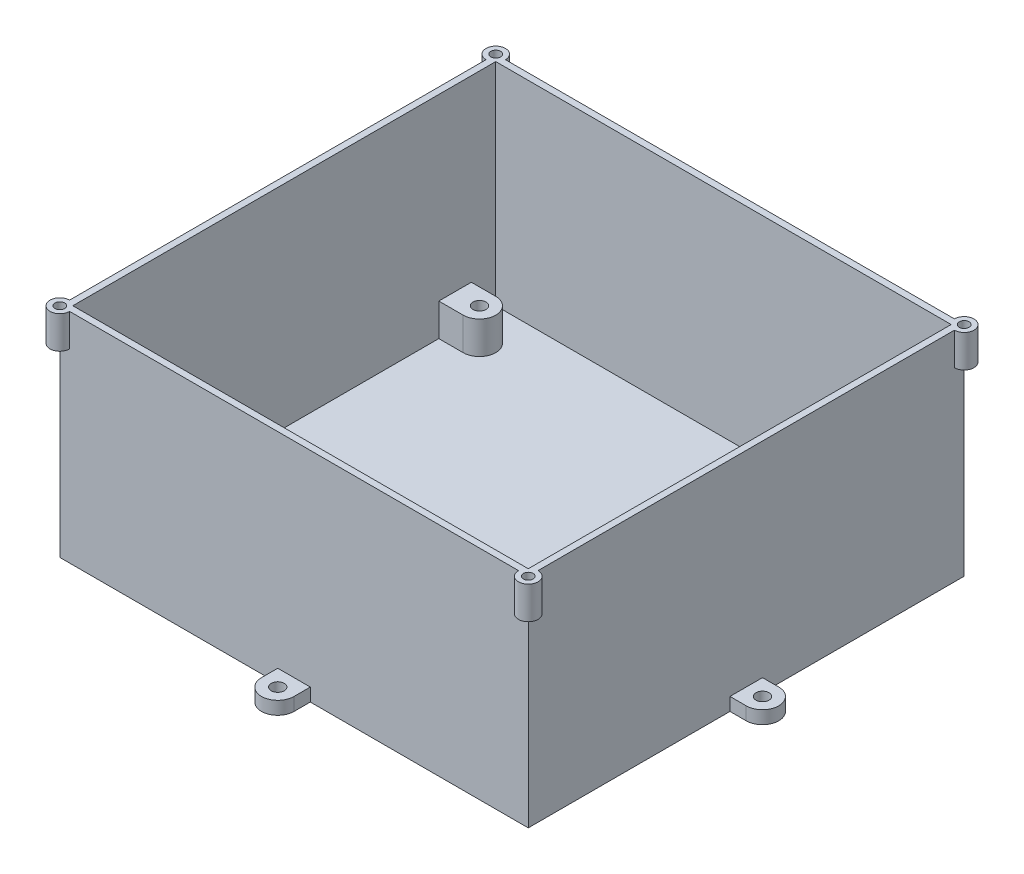
SolidWorks part; units mm, degrees
ref_plane "Front Plane" through (0, 0, 0) normal (0, 0, 1) x (1, 0, 0)
ref_plane "Top Plane" through (0, 0, 0) normal (0, 1, 0) x (1, 0, 0)
ref_plane "Right Plane" through (0, 0, 0) normal (1, 0, 0) x (0, 0, -1)
sketch "Sketch1" plane through (0, 0, 0) normal (0, 1, 0) x (1, 0, 0)
  line L0 (-72, 67) -> (-72, -67)
  line L1 (-70, 65) -> (70, 65)
  line L2 (-70, 65) -> (-70, 57.5)
  line L3 (-70, -65) -> (70, -65)
  line L4 (70, 65) -> (70, 57.5)
  line L5 (-62.5, 52.5) -> (-70, 52.5) construction
  line L6 (-67.5, 57.5) -> (67.5, 57.5) construction
  line L7 (-72, -67) -> (72, -67)
  line L8 (72, 67) -> (72, -67)
  line L9 (-72, 67) -> (72, 67)
  line L10 (-67.5, 57.5) -> (-67.5, -57.5) construction
  line L11 (-67.5, -57.5) -> (67.5, -57.5) construction
  line L12 (67.5, 57.5) -> (67.5, -57.5) construction
  line L13 (-67.5, 57.5) -> (67.5, -57.5) construction
  line L14 (-67.5, -57.5) -> (67.5, 57.5) construction
  line L15 (-62.5, 52.5) -> (-72, 52.5) construction
  line L16 (-62.5, 47.5) -> (-70, 47.5)
  line L17 (-62.5, 57.5) -> (-70, 57.5)
  line L18 (62.5, 52.5) -> (72, 52.5) construction
  line L19 (62.5, 57.5) -> (70, 57.5)
  line L20 (62.5, 47.5) -> (70, 47.5)
  line L21 (62.5, -52.5) -> (72, -52.5) construction
  line L22 (62.5, -47.5) -> (70, -47.5)
  line L23 (62.5, -57.5) -> (70, -57.5)
  line L24 (-62.5, -52.5) -> (-72, -52.5) construction
  line L25 (-62.5, -57.5) -> (-70, -57.5)
  line L26 (-62.5, -47.5) -> (-70, -47.5)
  line L27 (-70, 47.5) -> (-70, -47.5)
  line L28 (-70, 65) -> (-70, -65) construction
  line L29 (70, 47.5) -> (70, -47.5)
  line L30 (70, 65) -> (70, -65) construction
  line L31 (70, -57.5) -> (70, -65)
  line L32 (-70, -57.5) -> (-70, -65)
  circle A0 centre (-62.5, 52.5) radius 2
  circle A1 centre (62.5, 52.5) radius 2
  circle A2 centre (-62.5, -52.5) radius 2
  circle A3 centre (62.5, -52.5) radius 2
  arc A4 (-62.5, 47.5) -> (-62.5, 57.5) centre (-62.5, 52.5) ccw
  arc A6 (62.5, 57.5) -> (62.5, 47.5) centre (62.5, 52.5) ccw
  arc A8 (62.5, -47.5) -> (62.5, -57.5) centre (62.5, -52.5) ccw
  arc A10 (-62.5, -57.5) -> (-62.5, -47.5) centre (-62.5, -52.5) ccw
  point P0 (0, 0)
  point P18 (-67.25, 52.5)
  point P20 (0, 0)
  point P31 (67.25, 52.5)
  point P36 (67.25, -52.5)
  point P42 (-67.25, -52.5)
  dimension "D4" = 4
  dimension "D16" = 5
  dimension "D17" = 5
  dimension "D18" = 5
  dimension "D19" = 5
  dimension "D1" = 130
  dimension "D2" = 140
  dimension "D5" = 125
  dimension "D6" = 105
  dimension "D7" = 5
  dimension "D8" = 5
  dimension "D9" = 135
  dimension "D10" = 115
  dimension "D11" = 5
  dimension "D12" = 5
  dimension "D13" = 105
  dimension "D14" = 5
  dimension "D3" = 2
extrude "Boss-Extrude1" add sketch "Sketch1" along normal blind 55
sketch "Sketch2" plane through (0, 55, 0) normal (0, 1, 0) x (1, 0, 0)
  line L0 (-70, -47.5) -> (-62.5, -47.5) construction
  line L1 (-62.5, -57.5) -> (-70, -57.5) construction
  line L2 (70, -57.5) -> (62.5, -57.5) construction
  line L3 (62.5, -47.5) -> (70, -47.5) construction
  line L4 (70, 47.5) -> (62.5, 47.5) construction
  line L5 (62.5, 57.5) -> (70, 57.5) construction
  line L6 (-62.5, 47.5) -> (-70, 47.5) construction
  line L7 (-70, 57.5) -> (-62.5, 57.5) construction
  line L8 (-70, -47.5) -> (-62.5, -47.5)
  line L9 (-62.5, -57.5) -> (-70, -57.5)
  line L10 (70, -57.5) -> (62.5, -57.5)
  line L11 (62.5, -47.5) -> (70, -47.5)
  line L12 (70, 47.5) -> (62.5, 47.5)
  line L13 (62.5, 57.5) -> (70, 57.5)
  line L14 (-62.5, 47.5) -> (-70, 47.5)
  line L15 (-70, 57.5) -> (-62.5, 57.5)
  line L16 (-70, 57.5) -> (-70, 47.5)
  line L17 (70, 57.5) -> (70, 47.5)
  line L18 (70, -47.5) -> (70, -57.5)
  line L19 (-70, -47.5) -> (-70, -57.5)
  circle A0 centre (62.5, 52.5) radius 2 construction
  circle A1 centre (-62.5, 52.5) radius 2 construction
  circle A2 centre (-62.5, -52.5) radius 2 construction
  arc A3 (-62.5, -57.5) -> (-62.5, -47.5) centre (-62.5, -52.5) ccw construction
  circle A4 centre (62.5, -52.5) radius 2 construction
  arc A5 (62.5, -47.5) -> (62.5, -57.5) centre (62.5, -52.5) ccw construction
  arc A6 (62.5, 57.5) -> (62.5, 47.5) centre (62.5, 52.5) ccw construction
  arc A7 (-62.5, 47.5) -> (-62.5, 57.5) centre (-62.5, 52.5) ccw construction
  circle A8 centre (62.5, 52.5) radius 2
  circle A9 centre (-62.5, 52.5) radius 2
  circle A10 centre (-62.5, -52.5) radius 2
  arc A11 (-62.5, -57.5) -> (-62.5, -47.5) centre (-62.5, -52.5) ccw
  circle A12 centre (62.5, -52.5) radius 2
  arc A13 (62.5, -47.5) -> (62.5, -57.5) centre (62.5, -52.5) ccw
  arc A14 (62.5, 57.5) -> (62.5, 47.5) centre (62.5, 52.5) ccw
  arc A15 (-62.5, 47.5) -> (-62.5, 57.5) centre (-62.5, 52.5) ccw
extrude "Cut-Extrude1" cut sketch "Sketch2" against normal blind 45
sketch "Sketch3" plane through (0, 0, 0) normal (0, -1, 0) x (1, 0, 0)
  line L1 (-72, 67) -> (72, 67)
  line L2 (-72, 67) -> (-72, -67)
  line L3 (-72, -67) -> (72, -67)
  line L4 (72, 67) -> (72, -67)
extrude "Boss-Extrude2" add sketch "Sketch3" along normal blind 2
sketch "Sketch4" plane through (0, 0, 0) normal (0, 1, 0) x (1, 0, 0)
  line L0 (-87.4721, 0) -> (87.4721, 0) construction
  line L1 (0, 80.0878) -> (0, -80.0878) construction
  line L2 (72, 67) -> (-72, 67) construction
  line L3 (72, -67) -> (72, 67) construction
  line L4 (0, 72) -> (0, 65) construction
  line L5 (5, 72) -> (5, 65)
  line L6 (-5, 72) -> (-5, 65)
  line L7 (77, 0) -> (70, 0) construction
  line L8 (77, -5) -> (70, -5)
  line L9 (77, 5) -> (70, 5)
  line L10 (-5, 65) -> (5, 65)
  line L11 (70, 5) -> (70, -5)
  line L12 (-77, -5) -> (-70, -5)
  line L13 (-77, 5) -> (-70, 5)
  line L14 (-70, 5) -> (-70, -5)
  line L15 (-5, -65) -> (5, -65)
  line L16 (5, -72) -> (5, -65)
  line L17 (-5, -72) -> (-5, -65)
  circle A0 centre (0, 72) radius 2
  circle A1 centre (77, 0) radius 2
  arc A2 (5, 72) -> (-5, 72) centre (0, 72) ccw
  arc A4 (77, -5) -> (77, 5) centre (77, 0) ccw
  circle A6 centre (-77, 0) radius 2
  arc A7 (-77, -5) -> (-77, 5) centre (-77, 0) cw
  circle A8 centre (0, -72) radius 2
  arc A9 (5, -72) -> (-5, -72) centre (0, -72) cw
  point P4 (0, 0)
  point P8 (0, 0)
  point P16 (0, 68.5)
  point P23 (73.5, 0)
  dimension "D3" = 4
  dimension "D4" = 4
  dimension "D5" = 5
  dimension "D6" = 5
  dimension "D1" = 5
  dimension "D2" = 5
  dimension "D7" = 7
  dimension "D8" = 7
sketch "Sketch5" plane through (0, -2, 0) normal (0, -1, 0) x (1, 0, 0)
  line L0 (-70, -5) -> (-70, 5) construction
  line L1 (-77, 5) -> (-70, 5) construction
  line L2 (-77, -5) -> (-70, -5) construction
  line L3 (5, -72) -> (5, -65) construction
  line L4 (-5, -65) -> (5, -65) construction
  line L5 (-5, -72) -> (-5, -65) construction
  line L6 (70, -5) -> (70, 5) construction
  line L7 (77, 5) -> (70, 5) construction
  line L8 (77, -5) -> (70, -5) construction
  line L9 (-5, 65) -> (5, 65) construction
  line L10 (5, 72) -> (5, 65) construction
  line L11 (-5, 72) -> (-5, 65) construction
  line L12 (-70, -5) -> (-70, 5)
  line L13 (-77, 5) -> (-70, 5)
  line L14 (-77, -5) -> (-70, -5)
  line L15 (5, -72) -> (5, -65)
  line L16 (-5, -65) -> (5, -65)
  line L17 (-5, -72) -> (-5, -65)
  line L18 (70, -5) -> (70, 5)
  line L19 (77, 5) -> (70, 5)
  line L20 (77, -5) -> (70, -5)
  line L21 (-5, 65) -> (5, 65)
  line L22 (5, 72) -> (5, 65)
  line L23 (-5, 72) -> (-5, 65)
  arc A0 (-77, 5) -> (-77, -5) centre (-77, 0) ccw construction
  arc A1 (-5, -72) -> (5, -72) centre (0, -72) ccw construction
  circle A2 centre (77, 0) radius 2 construction
  arc A3 (77, -5) -> (77, 5) centre (77, 0) ccw construction
  circle A4 centre (0, 72) radius 2 construction
  arc A5 (5, 72) -> (-5, 72) centre (0, 72) ccw construction
  arc A6 (-77, 5) -> (-77, -5) centre (-77, 0) ccw
  arc A7 (-5, -72) -> (5, -72) centre (0, -72) ccw
  circle A8 centre (77, 0) radius 2
  arc A9 (77, -5) -> (77, 5) centre (77, 0) ccw
  circle A10 centre (0, 72) radius 2
  arc A11 (5, 72) -> (-5, 72) centre (0, 72) ccw
  circle A12 centre (-77, 0) radius 2 construction
  circle A13 centre (0, -72) radius 2 construction
  circle A14 centre (-77, 0) radius 2
  circle A15 centre (0, -72) radius 2
extrude "Boss-Extrude4" add sketch "Sketch5" against normal blind 4
sketch "Sketch6" plane through (0, 55, 0) normal (0, 1, 0) x (1, 0, 0)
  line L0 (72, 67) -> (-72, 67) construction
  line L1 (-72, -67) -> (72, -67) construction
  line L2 (72, -67) -> (72, 67) construction
  line L3 (-70, -65) -> (70, -65) construction
  line L4 (70, -65) -> (70, 65) construction
  line L5 (70, 65) -> (-70, 65) construction
  line L6 (-70, 65) -> (-70, -65) construction
  line L7 (-72, 67) -> (-72, -67) construction
  line L8 (72, 67) -> (-72, 67)
  line L9 (-72, -67) -> (72, -67)
  line L10 (72, -67) -> (72, 67)
  line L11 (-70, -65) -> (70, -65)
  line L12 (70, -65) -> (70, 65)
  line L13 (70, 65) -> (-70, 65)
  line L14 (-70, 65) -> (-70, -65)
  line L15 (-72, 67) -> (-72, -67)
extrude "Boss-Extrude5" add sketch "Sketch6" along normal blind 10
sketch "Sketch8" plane through (-72, 0, 0) normal (-1, 0, 0) x (0, 0, 1)
  line L0 (0, 0) -> (0, 72.1803) construction
  line L1 (0, 57.2077) -> (45, 57.2077) construction
  line L2 (0, 57.2077) -> (0, 11.2077) construction
  line L3 (0, 11.2077) -> (45, 11.2077) construction
  line L4 (45, 57.2077) -> (45, 11.2077) construction
  dimension "D1" = 45
  dimension "D2" = 46
  dimension "D3" = 0
sketch "Sketch11" plane through (0, 65, 0) normal (0, 1, 0) x (1, 0, 0)
  line L0 (-72, -67) -> (72, -67) construction
  line L1 (72, -67) -> (72, 67) construction
  line L2 (-72, 67) -> (-72, -67) construction
  line L3 (72, 67) -> (-72, 67) construction
  line L4 (-70.5, -67) -> (-69, -67)
  line L5 (72, -65.5) -> (72, -64)
  line L6 (-72, 65.5) -> (-72, 64)
  line L7 (70.5, 67) -> (69, 67)
  line L8 (69, -67) -> (70.5, -67)
  line L9 (72, 64) -> (72, 65.5)
  line L10 (-72, -64) -> (-72, -65.5)
  line L11 (-69, 67) -> (-70.5, 67)
  circle A0 centre (-72, 67) radius 1.5
  circle A1 centre (72, 67) radius 1.5
  circle A2 centre (-72, -67) radius 1.5
  circle A3 centre (72, -67) radius 1.5
  arc A4 (-69, 67) -> (-72, 64) centre (-72, 67) ccw
  arc A5 (72, 64) -> (69, 67) centre (72, 67) ccw
  arc A6 (69, -67) -> (72, -64) centre (72, -67) ccw
  arc A7 (-72, -64) -> (-69, -67) centre (-72, -67) ccw
  line M8 (72, -67) -> (72, 67)
  line M9 (72, 67) -> (-72, 67)
  line M10 (-72, 67) -> (-72, -67)
  line M11 (-72, -67) -> (72, -67)
  dimension "D1" = 3
  dimension "D2" = 6
extrude "Boss-Extrude11" add sketch "Sketch11" against normal blind 10 contours A4 A0 M9 M10 | A5 A1 M8 M9 | A6 A3 M11 M8 | A7 A2 M10 M11
sketch "Sketch12" plane through (0, 65, 0) normal (0, 1, 0) x (1, 0, 0)
  circle A0 centre (-72, 67) radius 1.5
  circle A1 centre (72, 67) radius 1.5
  circle A2 centre (72, -67) radius 1.5
  circle A3 centre (-72, -67) radius 1.5
extrude "Cut-Extrude3" cut sketch "Sketch12" against normal blind 10
